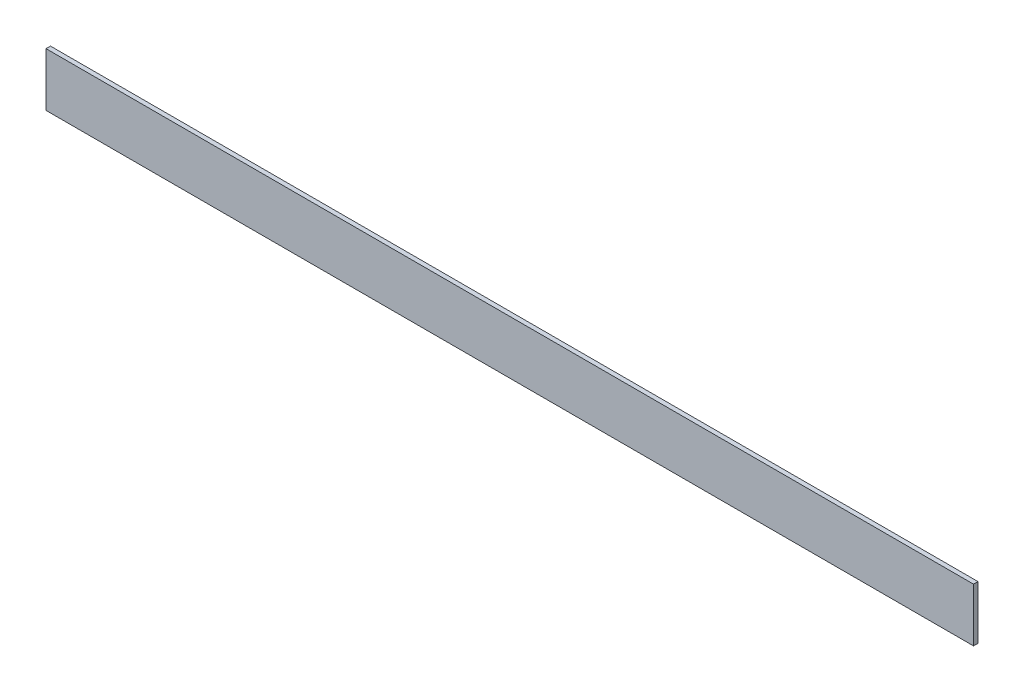
SolidWorks part; units mm, degrees
material "PVC 0.007 Plasticized"
ref_plane "Front Plane" through (0, 0, 0) normal (0, 0, 1) x (1, 0, 0)
ref_plane "Top Plane" through (0, 0, 0) normal (0, 1, 0) x (1, 0, 0)
ref_plane "Right Plane" through (0, 0, 0) normal (1, 0, 0) x (0, 0, -1)
sketch "Sketch1" plane through (0, 0, 0) normal (1, 0, 0) x (0, 0, -1)
  line L1 (-3.175, -38.1) -> (3.175, -38.1)
  line L2 (-3.175, -38.1) -> (-3.175, 38.1)
  line L3 (-3.175, 38.1) -> (3.175, 38.1)
  line L4 (3.175, -38.1) -> (3.175, 38.1)
  line L5 (-3.175, -38.1) -> (3.175, 38.1) construction
  line L6 (-3.175, 38.1) -> (3.175, -38.1) construction
  point P0 (0, 0)
  dimension "D1" = 76.2
  dimension "D2" = 6.35
extrude "Boss-Extrude1" add sketch "Sketch1" along normal blind 1320.8
equation "\"D2@Sketch1\"=1in/4"
